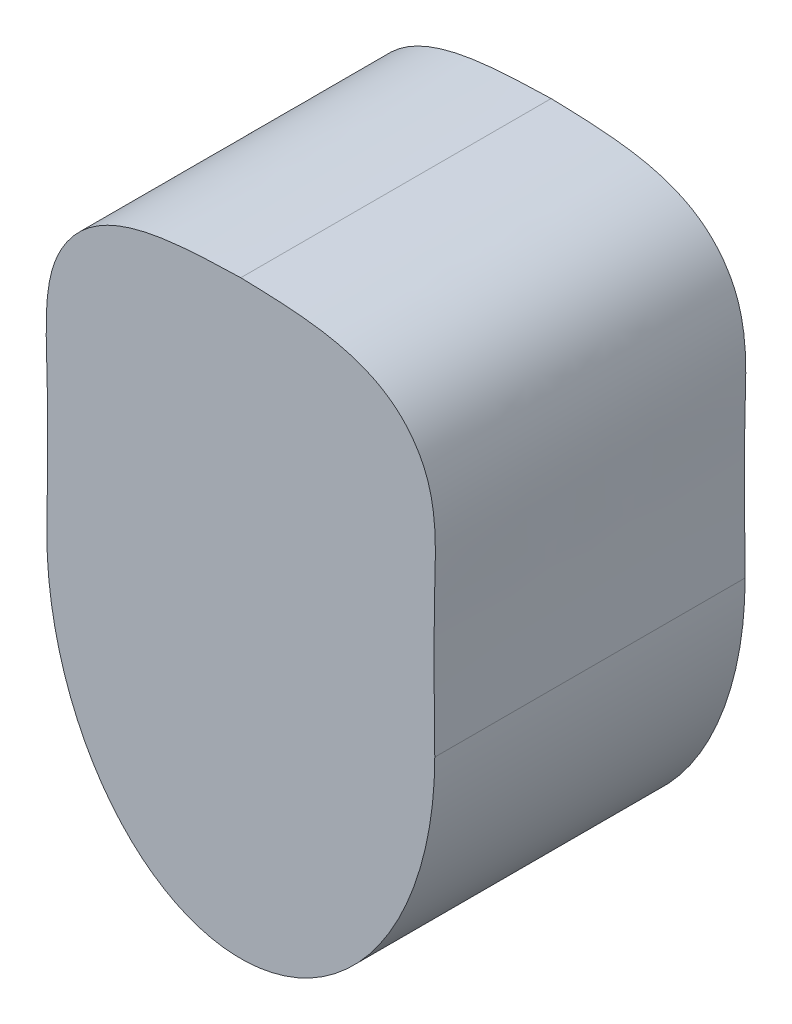
SolidWorks part; units mm, degrees
ref_plane "Front Plane" through (0, 0, 0) normal (0, 0, 1) x (1, 0, 0)
ref_plane "Top Plane" through (0, 0, 0) normal (0, 1, 0) x (1, 0, 0)
ref_plane "Right Plane" through (0, 0, 0) normal (1, 0, 0) x (0, 0, -1)
sketch "Sketch1" plane through (0, 0, 0) normal (0, 0, 1) x (1, 0, 0)
  line L0 (0, 0) -> (0, 82.0157) construction
  line L2 (50, 81.4757) -> (-50, 81.4757) construction
  line L3 (50, 81.4757) -> (50, -81.4757) construction
  line L4 (50, -81.4757) -> (-50, -81.4757) construction
  line L5 (-50, 81.4757) -> (-50, -81.4757) construction
  line L6 (50, 81.4757) -> (-50, -81.4757) construction
  line L7 (50, -81.4757) -> (-50, 81.4757) construction
  ellipse E0 centre (0, 0) end of major axis (0, 70) minor radius 50 (-50, 0) -> (50, 0) ccw
  spline S0 degree 3 poles (-50, 0) (-49.8243, 12.4411) (-49.526, 33.5575) (-50.8832, 58.6062) (-36.0319, 80.9901) (-16.6722, 81.5412) (0, 82.0157) knots 0 0 0 0 0.326036 0.553383 0.615382 1 1 1 1
  spline S1 degree 3 poles (50, 0) (49.8243, 12.4411) (49.526, 33.5575) (50.8832, 58.6062) (36.0319, 80.9901) (16.6722, 81.5412) (0, 82.0157) knots 0 0 0 0 0.326036 0.553383 0.615382 1 1 1 1
  dimension "D1" = 70
  dimension "D2" = 50
extrude "Extrude1" add sketch "Sketch1" along normal blind 80
